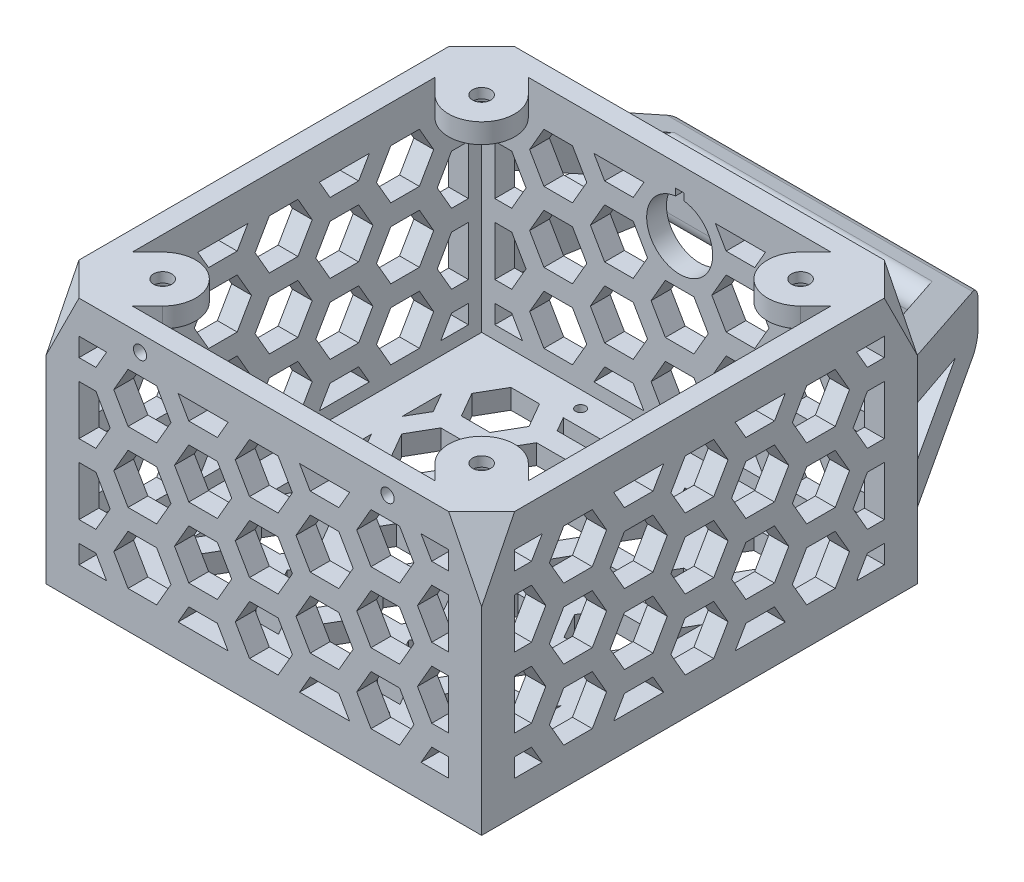
SolidWorks part; units mm, degrees
ref_plane "Front Plane" through (0, 0, 0) normal (0, 0, 1) x (1, 0, 0)
ref_plane "Top Plane" through (0, 0, 0) normal (0, 1, 0) x (1, 0, 0)
ref_plane "Right Plane" through (0, 0, 0) normal (1, 0, 0) x (0, 0, -1)
sketch "Sketch1" plane through (0, 0, 0) normal (0, 1, 0) x (1, 0, 0)
  line L0 (50, -50) -> (50, 50) construction
  line L1 (60, -60) -> (-60, -60)
  line L2 (60, -60) -> (60, 60)
  line L3 (60, 60) -> (-60, 60)
  line L4 (-60, -60) -> (-60, 60)
  line L5 (60, -60) -> (-60, 60) construction
  line L6 (60, 60) -> (-60, -60) construction
  line L7 (50, 50) -> (-50, 50) construction
  line L8 (-50, -50) -> (-50, 50) construction
  line L9 (50, -50) -> (-50, -50) construction
  line L10 (8.6603, 21.25) -> (4.3301, 28.75)
  line L11 (8.6603, 0) -> (4.3301, 7.5)
  line L12 (4.3301, 7.5) -> (-4.3301, 7.5)
  line L13 (-4.3301, 7.5) -> (-8.6603, 0)
  line L14 (-8.6603, 0) -> (-4.3301, -7.5)
  line L15 (-4.3301, -7.5) -> (4.3301, -7.5)
  line L16 (4.3301, -7.5) -> (8.6603, 0)
  line L17 (4.3301, 28.75) -> (-4.3301, 28.75)
  line L18 (-4.3301, 28.75) -> (-8.6603, 21.25)
  line L19 (-8.6603, 21.25) -> (-4.3301, 13.75)
  line L20 (-4.3301, 13.75) -> (4.3301, 13.75)
  line L21 (4.3301, 13.75) -> (8.6603, 21.25)
  line L22 (8.6603, 42.5) -> (4.3301, 50)
  line L23 (4.3301, 50) -> (-4.3301, 50)
  line L24 (-4.3301, 50) -> (-8.6603, 42.5)
  line L25 (-8.6603, 42.5) -> (-4.3301, 35)
  line L26 (-4.3301, 35) -> (4.3301, 35)
  line L27 (4.3301, 35) -> (8.6603, 42.5)
  line L28 (8.6603, -21.25) -> (4.3301, -13.75)
  line L29 (4.3301, -13.75) -> (-4.3301, -13.75)
  line L30 (-4.3301, -13.75) -> (-8.6603, -21.25)
  line L31 (-8.6603, -21.25) -> (-4.3301, -28.75)
  line L32 (-4.3301, -28.75) -> (4.3301, -28.75)
  line L33 (4.3301, -28.75) -> (8.6603, -21.25)
  line L34 (8.6603, -42.5) -> (4.3301, -35)
  line L35 (4.3301, -35) -> (-4.3301, -35)
  line L36 (-4.3301, -35) -> (-8.6603, -42.5)
  line L37 (-8.6603, -42.5) -> (-4.3301, -50)
  line L38 (-4.3301, -50) -> (4.3301, -50)
  line L39 (4.3301, -50) -> (8.6603, -42.5)
  line L40 (0, 13.75) -> (0, 7.5) construction
  line L41 (0, 10.625) -> (50, 10.625) construction
  line L42 (27.0633, 31.875) -> (22.7332, 39.375)
  line L43 (27.0633, 10.625) -> (22.7332, 18.125)
  line L44 (22.7332, 18.125) -> (14.0729, 18.125)
  line L45 (14.0729, 18.125) -> (9.7428, 10.625)
  line L46 (9.7428, 10.625) -> (14.0729, 3.125)
  line L47 (14.0729, 3.125) -> (22.7332, 3.125)
  line L48 (22.7332, 3.125) -> (27.0633, 10.625)
  line L49 (22.7332, 39.375) -> (14.0729, 39.375)
  line L50 (14.0729, 39.375) -> (9.7428, 31.875)
  line L51 (9.7428, 31.875) -> (14.0729, 24.375)
  line L52 (14.0729, 24.375) -> (22.7332, 24.375)
  line L53 (22.7332, 24.375) -> (27.0633, 31.875)
  line L57 (11.547, 50) -> (14.0729, 45.625)
  line L58 (14.0729, 45.625) -> (22.7332, 45.625)
  line L59 (22.7332, 45.625) -> (25.2591, 50)
  line L60 (22.7332, 60.625) -> (14.0729, 60.625)
  line L61 (14.0729, 60.625) -> (13.7121, 60)
  line L62 (23.094, 60) -> (22.7332, 60.625)
  line L63 (11.547, 50) -> (25.2591, 50)
  line L64 (-60, 0) -> (60, 0) construction
  line L65 (0, 60) -> (0, -60) construction
  line L66 (11.547, -50) -> (14.0729, -45.625)
  line L67 (14.0729, -45.625) -> (22.7332, -45.625)
  line L68 (22.7332, -45.625) -> (25.2591, -50)
  line L69 (11.547, -50) -> (25.2591, -50)
  line L70 (22.7332, -24.375) -> (27.0633, -31.875)
  line L71 (14.0729, -24.375) -> (22.7332, -24.375)
  line L72 (9.7428, -31.875) -> (14.0729, -24.375)
  line L73 (14.0729, -39.375) -> (9.7428, -31.875)
  line L74 (22.7332, -39.375) -> (14.0729, -39.375)
  line L75 (27.0633, -31.875) -> (22.7332, -39.375)
  line L76 (22.7332, -3.125) -> (27.0633, -10.625)
  line L77 (14.0729, -3.125) -> (22.7332, -3.125)
  line L78 (9.7428, -10.625) -> (14.0729, -3.125)
  line L79 (14.0729, -18.125) -> (9.7428, -10.625)
  line L80 (22.7332, -18.125) -> (14.0729, -18.125)
  line L81 (27.0633, -10.625) -> (22.7332, -18.125)
  line L82 (45.4663, 42.5) -> (41.1362, 50)
  line L83 (41.1362, 50) -> (32.476, 50)
  line L84 (32.476, 50) -> (28.1458, 42.5)
  line L85 (28.1458, 42.5) -> (32.476, 35)
  line L86 (32.476, 35) -> (41.1362, 35)
  line L87 (41.1362, 35) -> (45.4663, 42.5)
  line L88 (45.4663, 21.25) -> (41.1362, 28.75)
  line L89 (41.1362, 28.75) -> (32.476, 28.75)
  line L90 (32.476, 28.75) -> (28.1458, 21.25)
  line L91 (28.1458, 21.25) -> (32.476, 13.75)
  line L92 (32.476, 13.75) -> (41.1362, 13.75)
  line L93 (41.1362, 13.75) -> (45.4663, 21.25)
  line L94 (45.4663, 0) -> (41.1362, 7.5)
  line L95 (41.1362, 7.5) -> (32.476, 7.5)
  line L96 (32.476, 7.5) -> (28.1458, 0)
  line L97 (28.1458, 0) -> (32.476, -7.5)
  line L98 (32.476, -7.5) -> (41.1362, -7.5)
  line L99 (41.1362, -7.5) -> (45.4663, 0)
  line L100 (45.4663, -21.25) -> (41.1362, -13.75)
  line L101 (41.1362, -13.75) -> (32.476, -13.75)
  line L102 (32.476, -13.75) -> (28.1458, -21.25)
  line L103 (28.1458, -21.25) -> (32.476, -28.75)
  line L104 (32.476, -28.75) -> (41.1362, -28.75)
  line L105 (41.1362, -28.75) -> (45.4663, -21.25)
  line L106 (45.4663, -42.5) -> (41.1362, -35)
  line L107 (41.1362, -35) -> (32.476, -35)
  line L108 (32.476, -35) -> (28.1458, -42.5)
  line L109 (28.1458, -42.5) -> (32.476, -50)
  line L110 (32.476, -50) -> (41.1362, -50)
  line L111 (41.1362, -50) -> (45.4663, -42.5)
  line L118 (50, 37.8525) -> (46.5489, 31.875)
  line L119 (46.5489, 31.875) -> (50, 25.8975)
  line L124 (50, 16.6025) -> (46.5489, 10.625)
  line L125 (46.5489, 10.625) -> (50, 4.6475)
  line L131 (50, -16.6025) -> (46.5489, -10.625)
  line L132 (46.5489, -10.625) -> (50, -4.6475)
  line L137 (50, -37.8525) -> (46.5489, -31.875)
  line L138 (46.5489, -31.875) -> (50, -25.8975)
  line L144 (50, 37.8525) -> (50, 25.8975)
  line L145 (50.879, 45.625) -> (59.5392, 45.625)
  line L146 (59.5392, 45.625) -> (60, 46.423)
  line L147 (50.879, 24.375) -> (59.5392, 24.375)
  line L148 (59.5392, 39.375) -> (50.879, 39.375)
  line L149 (63.8694, 31.875) -> (60, 38.577)
  line L150 (60, 25.173) -> (63.8694, 31.875)
  line L151 (59.5392, 18.125) -> (50.879, 18.125)
  line L152 (50.879, 3.125) -> (59.5392, 3.125)
  line L153 (63.8694, 10.625) -> (60, 17.327)
  line L154 (59.5392, 3.125) -> (60, 3.923)
  line L155 (59.5392, -18.125) -> (50.879, -18.125)
  line L156 (50.879, -3.125) -> (59.5392, -3.125)
  line L157 (60, -3.923) -> (63.8694, -10.625)
  line L158 (60, -17.327) -> (59.5392, -18.125)
  line L159 (59.5392, -39.375) -> (50.879, -39.375)
  line L160 (50.879, -24.375) -> (59.5392, -24.375)
  line L161 (60, -25.173) -> (63.8694, -31.875)
  line L162 (63.8694, -31.875) -> (60, -38.577)
  line L163 (50.879, -45.625) -> (59.5392, -45.625)
  line L164 (59.5392, -45.625) -> (60, -46.423)
  line L165 (48.3531, 50) -> (50, 47.1475)
  line L166 (47.1304, 50) -> (50, 50)
  line L167 (50, 16.6025) -> (50, 4.6475)
  line L168 (50, -4.6475) -> (50, -16.6025)
  line L169 (50, -25.8975) -> (50, -37.8525)
  line L170 (-46.5489, -31.875) -> (-50, -25.8975)
  line L171 (48.3531, -50) -> (48.9559, -48.9559)
  line L172 (48.3531, -50) -> (50, -50)
  line L173 (-50, -37.8525) -> (-46.5489, -31.875)
  line L174 (-50, -25.8975) -> (-50, -37.8525)
  line L175 (-46.5489, -10.625) -> (-50, -4.6475)
  line L176 (-50, -16.6025) -> (-46.5489, -10.625)
  line L177 (-50, -4.6475) -> (-50, -16.6025)
  line L178 (-50, 16.6025) -> (-46.5489, 10.625)
  line L179 (-46.5489, 10.625) -> (-50, 4.6475)
  line L180 (-50, 16.6025) -> (-50, 4.6475)
  line L181 (-50, 37.8525) -> (-46.5489, 31.875)
  line L182 (-46.5489, 31.875) -> (-50, 25.8975)
  line L183 (-50, 37.8525) -> (-50, 25.8975)
  line L184 (-41.1362, 35) -> (-45.4663, 42.5)
  line L185 (-32.476, 35) -> (-41.1362, 35)
  line L186 (-28.1458, 42.5) -> (-32.476, 35)
  line L187 (-32.476, 50) -> (-28.1458, 42.5)
  line L188 (-41.1362, 50) -> (-32.476, 50)
  line L189 (-45.4663, 42.5) -> (-41.1362, 50)
  line L190 (-41.1362, 13.75) -> (-45.4663, 21.25)
  line L191 (-32.476, 13.75) -> (-41.1362, 13.75)
  line L192 (-28.1458, 21.25) -> (-32.476, 13.75)
  line L193 (-32.476, 28.75) -> (-28.1458, 21.25)
  line L194 (-41.1362, 28.75) -> (-32.476, 28.75)
  line L195 (-45.4663, 21.25) -> (-41.1362, 28.75)
  line L196 (-41.1362, -7.5) -> (-45.4663, 0)
  line L197 (-32.476, -7.5) -> (-41.1362, -7.5)
  line L198 (-28.1458, 0) -> (-32.476, -7.5)
  line L199 (-32.476, 7.5) -> (-28.1458, 0)
  line L200 (-41.1362, 7.5) -> (-32.476, 7.5)
  line L201 (-45.4663, 0) -> (-41.1362, 7.5)
  line L202 (-41.1362, -28.75) -> (-45.4663, -21.25)
  line L203 (-32.476, -28.75) -> (-41.1362, -28.75)
  line L204 (-28.1458, -21.25) -> (-32.476, -28.75)
  line L205 (-32.476, -13.75) -> (-28.1458, -21.25)
  line L206 (-41.1362, -13.75) -> (-32.476, -13.75)
  line L207 (-45.4663, -21.25) -> (-41.1362, -13.75)
  line L208 (-41.1362, -50) -> (-45.4663, -42.5)
  line L209 (-32.476, -50) -> (-41.1362, -50)
  line L210 (-28.1458, -42.5) -> (-32.476, -50)
  line L211 (-32.476, -35) -> (-28.1458, -42.5)
  line L212 (-41.1362, -35) -> (-32.476, -35)
  line L213 (-45.4663, -42.5) -> (-41.1362, -35)
  line L214 (-11.547, -50) -> (-25.2591, -50)
  line L215 (-22.7332, -45.625) -> (-25.2591, -50)
  line L216 (-14.0729, -45.625) -> (-22.7332, -45.625)
  line L217 (-11.547, -50) -> (-14.0729, -45.625)
  line L218 (-14.0729, -24.375) -> (-22.7332, -24.375)
  line L219 (-9.7428, -31.875) -> (-14.0729, -24.375)
  line L220 (-14.0729, -39.375) -> (-9.7428, -31.875)
  line L221 (-22.7332, -39.375) -> (-14.0729, -39.375)
  line L222 (-27.0633, -31.875) -> (-22.7332, -39.375)
  line L223 (-22.7332, -24.375) -> (-27.0633, -31.875)
  line L224 (-14.0729, -3.125) -> (-22.7332, -3.125)
  line L225 (-9.7428, -10.625) -> (-14.0729, -3.125)
  line L226 (-14.0729, -18.125) -> (-9.7428, -10.625)
  line L227 (-22.7332, -18.125) -> (-14.0729, -18.125)
  line L228 (-27.0633, -10.625) -> (-22.7332, -18.125)
  line L229 (-22.7332, -3.125) -> (-27.0633, -10.625)
  line L230 (-22.7332, 3.125) -> (-27.0633, 10.625)
  line L231 (-14.0729, 3.125) -> (-22.7332, 3.125)
  line L232 (-9.7428, 10.625) -> (-14.0729, 3.125)
  line L233 (-14.0729, 18.125) -> (-9.7428, 10.625)
  line L234 (-22.7332, 18.125) -> (-14.0729, 18.125)
  line L235 (-27.0633, 10.625) -> (-22.7332, 18.125)
  line L236 (-11.547, 50) -> (-14.0729, 45.625)
  line L237 (-14.0729, 45.625) -> (-22.7332, 45.625)
  line L238 (-22.7332, 45.625) -> (-25.2591, 50)
  line L239 (-11.547, 50) -> (-25.2591, 50)
  line L240 (-22.7332, 24.375) -> (-27.0633, 31.875)
  line L241 (-14.0729, 24.375) -> (-22.7332, 24.375)
  line L242 (-9.7428, 31.875) -> (-14.0729, 24.375)
  line L243 (-14.0729, 39.375) -> (-9.7428, 31.875)
  line L244 (-22.7332, 39.375) -> (-14.0729, 39.375)
  line L245 (-27.0633, 31.875) -> (-22.7332, 39.375)
  circle A0 centre (0, 0) radius 7.5 construction
  circle A1 centre (18.403, 10.625) radius 7.5 construction
  point P0 (0, 0)
  point P265 (0, 0)
  dimension "D1" = 120
  dimension "D2" = 120
  dimension "D4" = 15
  dimension "D6" = 0
  dimension "D7" = 3
  dimension "D8" = 0
  dimension "D9" = 15
  dimension "D10" = 6.25
  dimension "D12" = 6.25
  dimension "D14" = 6.25
  dimension "D16" = 6.25
  dimension "D3" = 10
  dimension "D5" = 3
  dimension "D11" = 3
  dimension "D13" = 2
  dimension "D15" = 2
extrude "Boss-Extrude2" add sketch "Sketch1" along normal blind 6
sketch "Sketch2" plane through (0, 0, 60) normal (0, 0, 1) x (1, 0, 0)
  line L0 (0, 0) -> (0, 80) construction
  line L1 (-66, 40) -> (66, 40) construction
  line L2 (66, 80) -> (-66, 80)
  line L3 (66, 80) -> (66, 0)
  line L4 (66, 0) -> (-66, 0)
  line L5 (-66, 80) -> (-66, 0)
  line L6 (66, 80) -> (-66, 0) construction
  line L7 (66, 0) -> (-66, 80) construction
  line L8 (56, 70) -> (56, 10) construction
  line L9 (56, 10) -> (-56, 10) construction
  line L10 (-56, 70) -> (-56, 10) construction
  line L11 (56, 70) -> (-56, 70) construction
  line L12 (8.6603, 61.25) -> (4.3301, 68.75)
  line L13 (8.6603, 40) -> (4.3301, 47.5)
  line L14 (4.3301, 47.5) -> (-4.3301, 47.5)
  line L15 (-4.3301, 47.5) -> (-8.6603, 40)
  line L16 (-8.6603, 40) -> (-4.3301, 32.5)
  line L17 (-4.3301, 32.5) -> (4.3301, 32.5)
  line L18 (4.3301, 32.5) -> (8.6603, 40)
  line L19 (4.3301, 68.75) -> (-4.3301, 68.75)
  line L20 (-4.3301, 68.75) -> (-8.6603, 61.25)
  line L21 (-8.6603, 61.25) -> (-4.3301, 53.75)
  line L22 (-4.3301, 53.75) -> (4.3301, 53.75)
  line L23 (4.3301, 53.75) -> (8.6603, 61.25)
  line L24 (4.3301, 26.25) -> (8.6603, 18.75)
  line L25 (-4.3301, 26.25) -> (4.3301, 26.25)
  line L26 (-8.6603, 18.75) -> (-4.3301, 26.25)
  line L27 (-4.3301, 11.25) -> (-8.6603, 18.75)
  line L28 (4.3301, 11.25) -> (-4.3301, 11.25)
  line L29 (8.6603, 18.75) -> (4.3301, 11.25)
  line L30 (0, 53.75) -> (0, 47.5) construction
  line L31 (0, 50.625) -> (56, 50.625) construction
  line L32 (-60, 6) -> (-60, 0) construction
  line L33 (27.0633, 50.625) -> (22.7332, 58.125)
  line L34 (22.7332, 58.125) -> (14.0729, 58.125)
  line L35 (14.0729, 58.125) -> (9.7428, 50.625)
  line L36 (9.7428, 50.625) -> (14.0729, 43.125)
  line L37 (14.0729, 43.125) -> (22.7332, 43.125)
  line L38 (22.7332, 43.125) -> (27.0633, 50.625)
  line L39 (-60, 0) -> (60, 0) construction
  line L43 (10.8253, 70) -> (14.0729, 64.375)
  line L44 (14.0729, 64.375) -> (22.7332, 64.375)
  line L45 (22.7332, 64.375) -> (25.9808, 70)
  line L46 (14.0729, 79.375) -> (9.7428, 71.875)
  line L47 (22.7332, 79.375) -> (14.0729, 79.375)
  line L48 (27.0633, 71.875) -> (22.7332, 79.375)
  line L49 (10.8253, 70) -> (25.9808, 70)
  line L50 (22.7332, 36.875) -> (27.0633, 29.375)
  line L51 (14.0729, 36.875) -> (22.7332, 36.875)
  line L52 (9.7428, 29.375) -> (14.0729, 36.875)
  line L53 (14.0729, 21.875) -> (9.7428, 29.375)
  line L54 (22.7332, 21.875) -> (14.0729, 21.875)
  line L55 (27.0633, 29.375) -> (22.7332, 21.875)
  line L56 (10.8253, 10) -> (14.0729, 15.625)
  line L57 (14.0729, 15.625) -> (22.7332, 15.625)
  line L58 (22.7332, 15.625) -> (25.9808, 10)
  line L59 (10.8253, 10) -> (25.9808, 10)
  line L60 (45.4663, 61.25) -> (41.1362, 68.75)
  line L61 (41.1362, 68.75) -> (32.476, 68.75)
  line L62 (32.476, 68.75) -> (28.1458, 61.25)
  line L63 (28.1458, 61.25) -> (32.476, 53.75)
  line L64 (32.476, 53.75) -> (41.1362, 53.75)
  line L65 (41.1362, 53.75) -> (45.4663, 61.25)
  line L66 (45.4663, 40) -> (41.1362, 47.5)
  line L67 (41.1362, 47.5) -> (32.476, 47.5)
  line L68 (32.476, 47.5) -> (28.1458, 40)
  line L69 (28.1458, 40) -> (32.476, 32.5)
  line L70 (32.476, 32.5) -> (41.1362, 32.5)
  line L71 (41.1362, 32.5) -> (45.4663, 40)
  line L72 (41.1362, 26.25) -> (45.4663, 18.75)
  line L73 (45.4663, 18.75) -> (41.1362, 11.25)
  line L74 (41.1362, 11.25) -> (32.476, 11.25)
  line L75 (32.476, 11.25) -> (28.1458, 18.75)
  line L76 (28.1458, 18.75) -> (32.476, 26.25)
  line L77 (32.476, 26.25) -> (41.1362, 26.25)
  line L78 (47.6314, 70) -> (56, 70)
  line L80 (50.879, 64.375) -> (56, 64.375)
  line L81 (47.6314, 70) -> (50.879, 64.375)
  line L83 (56, 58.125) -> (50.879, 58.125)
  line L84 (50.879, 58.125) -> (46.5489, 50.625)
  line L85 (46.5489, 50.625) -> (50.879, 43.125)
  line L86 (50.879, 43.125) -> (56, 43.125)
  line L90 (56, 21.875) -> (50.879, 21.875)
  line L91 (50.879, 21.875) -> (46.5489, 29.375)
  line L92 (46.5489, 29.375) -> (50.879, 36.875)
  line L93 (50.879, 36.875) -> (56, 36.875)
  line L94 (47.6314, 10) -> (50.879, 15.625)
  line L95 (50.879, 15.625) -> (56, 15.625)
  line L97 (47.6314, 10) -> (56, 10)
  line L98 (59.5392, 64.375) -> (62.7868, 70)
  line L99 (63.8694, 50.625) -> (59.5392, 58.125)
  line L100 (59.5392, 43.125) -> (63.8694, 50.625)
  line L101 (56, 70) -> (56, 64.375)
  line L102 (56, 58.125) -> (56, 43.125)
  line L103 (56, 36.875) -> (56, 21.875)
  line L104 (59.5392, 36.875) -> (63.8694, 29.375)
  line L105 (63.8694, 29.375) -> (59.5392, 21.875)
  line L106 (59.5392, 15.625) -> (62.7868, 10)
  line L107 (56, 15.625) -> (56, 10)
  line L108 (-50.879, 15.625) -> (-56, 15.625)
  line L109 (-47.6314, 10) -> (-50.879, 15.625)
  line L110 (-47.6314, 10) -> (-56, 10)
  line L111 (-56, 15.625) -> (-56, 10)
  line L112 (-50.879, 36.875) -> (-56, 36.875)
  line L113 (-46.5489, 29.375) -> (-50.879, 36.875)
  line L114 (-50.879, 21.875) -> (-46.5489, 29.375)
  line L115 (-56, 21.875) -> (-50.879, 21.875)
  line L116 (-56, 36.875) -> (-56, 21.875)
  line L117 (-56, 58.125) -> (-50.879, 58.125)
  line L118 (-50.879, 58.125) -> (-46.5489, 50.625)
  line L119 (-46.5489, 50.625) -> (-50.879, 43.125)
  line L120 (-50.879, 43.125) -> (-56, 43.125)
  line L121 (-56, 58.125) -> (-56, 43.125)
  line L122 (-47.6314, 70) -> (-56, 70)
  line L123 (-47.6314, 70) -> (-50.879, 64.375)
  line L124 (-50.879, 64.375) -> (-56, 64.375)
  line L125 (-56, 70) -> (-56, 64.375)
  line L126 (-41.1362, 53.75) -> (-45.4663, 61.25)
  line L127 (-32.476, 53.75) -> (-41.1362, 53.75)
  line L128 (-28.1458, 61.25) -> (-32.476, 53.75)
  line L129 (-32.476, 68.75) -> (-28.1458, 61.25)
  line L130 (-41.1362, 68.75) -> (-32.476, 68.75)
  line L131 (-45.4663, 61.25) -> (-41.1362, 68.75)
  line L132 (-41.1362, 32.5) -> (-45.4663, 40)
  line L133 (-32.476, 32.5) -> (-41.1362, 32.5)
  line L134 (-28.1458, 40) -> (-32.476, 32.5)
  line L135 (-32.476, 47.5) -> (-28.1458, 40)
  line L136 (-41.1362, 47.5) -> (-32.476, 47.5)
  line L137 (-45.4663, 40) -> (-41.1362, 47.5)
  line L138 (-32.476, 26.25) -> (-41.1362, 26.25)
  line L139 (-28.1458, 18.75) -> (-32.476, 26.25)
  line L140 (-32.476, 11.25) -> (-28.1458, 18.75)
  line L141 (-41.1362, 11.25) -> (-32.476, 11.25)
  line L142 (-45.4663, 18.75) -> (-41.1362, 11.25)
  line L143 (-41.1362, 26.25) -> (-45.4663, 18.75)
  line L144 (-10.8253, 10) -> (-25.9808, 10)
  line L145 (-22.7332, 15.625) -> (-25.9808, 10)
  line L146 (-14.0729, 15.625) -> (-22.7332, 15.625)
  line L147 (-10.8253, 10) -> (-14.0729, 15.625)
  line L148 (-14.0729, 36.875) -> (-22.7332, 36.875)
  line L149 (-9.7428, 29.375) -> (-14.0729, 36.875)
  line L150 (-14.0729, 21.875) -> (-9.7428, 29.375)
  line L151 (-22.7332, 21.875) -> (-14.0729, 21.875)
  line L152 (-27.0633, 29.375) -> (-22.7332, 21.875)
  line L153 (-22.7332, 36.875) -> (-27.0633, 29.375)
  line L154 (-22.7332, 43.125) -> (-27.0633, 50.625)
  line L155 (-14.0729, 43.125) -> (-22.7332, 43.125)
  line L156 (-9.7428, 50.625) -> (-14.0729, 43.125)
  line L157 (-14.0729, 58.125) -> (-9.7428, 50.625)
  line L158 (-22.7332, 58.125) -> (-14.0729, 58.125)
  line L159 (-27.0633, 50.625) -> (-22.7332, 58.125)
  line L160 (-10.8253, 70) -> (-14.0729, 64.375)
  line L161 (-14.0729, 64.375) -> (-22.7332, 64.375)
  line L162 (-22.7332, 64.375) -> (-25.9808, 70)
  line L163 (-10.8253, 70) -> (-25.9808, 70)
  circle A0 centre (0, 40) radius 7.5 construction
  circle A1 centre (18.403, 50.625) radius 7.5 construction
  point P3 (0, 40)
  dimension "D1" = 80
  dimension "D3" = 15
  dimension "D5" = 6.25
  dimension "D6" = 15
  dimension "D7" = 6.25
  dimension "D8" = 6
  dimension "D10" = 6.25
  dimension "D12" = 6.25
  dimension "D14" = 6.25
  dimension "D2" = 10
  dimension "D4" = 2
  dimension "D9" = 2
  dimension "D11" = 2
  dimension "D13" = 2
extrude "Boss-Extrude3" add sketch "Sketch2" along normal blind 6
mirror "Mirror1" about plane through (0, 0, 0) normal (0, 0, 1) of "Boss-Extrude3"
sketch "Sketch3" plane through (-60, 0, 0) normal (-1, 0, 0) x (0, 0, 1)
  line L0 (-66, 80) -> (66, 80) construction
  line L1 (66, 80) -> (66, 0) construction
  line L2 (0, 0) -> (0, 80) construction
  line L3 (-66, 80) -> (-66, 0) construction
  line L4 (60, 0) -> (-60, 0)
  line L5 (60, 0) -> (60, 80)
  line L6 (60, 80) -> (-60, 80)
  line L7 (-60, 0) -> (-60, 80)
  line L8 (60, 0) -> (-60, 80) construction
  line L9 (60, 80) -> (-60, 0) construction
  line L10 (56, 10) -> (-56, 10) construction
  line L11 (56, 10) -> (56, 70) construction
  line L12 (56, 70) -> (-56, 70) construction
  line L13 (-56, 10) -> (-56, 70) construction
  line L14 (56, 10) -> (-56, 70) construction
  line L15 (56, 70) -> (-56, 10) construction
  line L16 (-66, 40) -> (66, 40) construction
  line L17 (8.6603, 40) -> (4.3301, 47.5)
  line L18 (4.3301, 47.5) -> (-4.3301, 47.5)
  line L19 (-4.3301, 47.5) -> (-8.6603, 40)
  line L20 (-8.6603, 40) -> (-4.3301, 32.5)
  line L21 (-4.3301, 32.5) -> (4.3301, 32.5)
  line L22 (4.3301, 32.5) -> (8.6603, 40)
  line L23 (8.6603, 61.25) -> (4.3301, 68.75)
  line L24 (4.3301, 68.75) -> (-4.3301, 68.75)
  line L25 (-4.3301, 68.75) -> (-8.6603, 61.25)
  line L26 (-8.6603, 61.25) -> (-4.3301, 53.75)
  line L27 (-4.3301, 53.75) -> (4.3301, 53.75)
  line L28 (4.3301, 53.75) -> (8.6603, 61.25)
  line L29 (4.3301, 26.25) -> (8.6603, 18.75)
  line L30 (-4.3301, 26.25) -> (4.3301, 26.25)
  line L31 (-8.6603, 18.75) -> (-4.3301, 26.25)
  line L32 (-4.3301, 11.25) -> (-8.6603, 18.75)
  line L33 (4.3301, 11.25) -> (-4.3301, 11.25)
  line L34 (8.6603, 18.75) -> (4.3301, 11.25)
  line L35 (0, 53.75) -> (0, 47.5) construction
  line L36 (0, 50.625) -> (56, 50.625) construction
  line L38 (27.0633, 50.625) -> (22.7332, 58.125)
  line L39 (22.7332, 58.125) -> (14.0729, 58.125)
  line L40 (14.0729, 58.125) -> (9.7428, 50.625)
  line L41 (9.7428, 50.625) -> (14.0729, 43.125)
  line L42 (14.0729, 43.125) -> (22.7332, 43.125)
  line L43 (22.7332, 43.125) -> (27.0633, 50.625)
  line L46 (10.8253, 70) -> (14.0729, 64.375)
  line L47 (14.0729, 64.375) -> (22.7332, 64.375)
  line L48 (22.7332, 64.375) -> (25.9808, 70)
  line L49 (14.0729, 79.375) -> (9.7428, 71.875)
  line L50 (22.7332, 79.375) -> (14.0729, 79.375)
  line L51 (27.0633, 71.875) -> (22.7332, 79.375)
  line L52 (10.8253, 70) -> (25.9808, 70)
  line L53 (22.7332, 36.875) -> (27.0633, 29.375)
  line L54 (14.0729, 36.875) -> (22.7332, 36.875)
  line L55 (9.7428, 29.375) -> (14.0729, 36.875)
  line L56 (14.0729, 21.875) -> (9.7428, 29.375)
  line L57 (22.7332, 21.875) -> (14.0729, 21.875)
  line L58 (27.0633, 29.375) -> (22.7332, 21.875)
  line L59 (10.8253, 10) -> (14.0729, 15.625)
  line L60 (14.0729, 15.625) -> (22.7332, 15.625)
  line L61 (22.7332, 15.625) -> (25.9808, 10)
  line L62 (10.8253, 10) -> (25.9808, 10)
  line L63 (45.4663, 61.25) -> (41.1362, 68.75)
  line L64 (41.1362, 68.75) -> (32.476, 68.75)
  line L65 (32.476, 68.75) -> (28.1458, 61.25)
  line L66 (28.1458, 61.25) -> (32.476, 53.75)
  line L67 (32.476, 53.75) -> (41.1362, 53.75)
  line L68 (41.1362, 53.75) -> (45.4663, 61.25)
  line L69 (45.4663, 40) -> (41.1362, 47.5)
  line L70 (41.1362, 47.5) -> (32.476, 47.5)
  line L71 (32.476, 47.5) -> (28.1458, 40)
  line L72 (28.1458, 40) -> (32.476, 32.5)
  line L73 (32.476, 32.5) -> (41.1362, 32.5)
  line L74 (41.1362, 32.5) -> (45.4663, 40)
  line L75 (41.1362, 26.25) -> (45.4663, 18.75)
  line L76 (45.4663, 18.75) -> (41.1362, 11.25)
  line L77 (41.1362, 11.25) -> (32.476, 11.25)
  line L78 (32.476, 11.25) -> (28.1458, 18.75)
  line L79 (28.1458, 18.75) -> (32.476, 26.25)
  line L80 (32.476, 26.25) -> (41.1362, 26.25)
  line L81 (47.6314, 70) -> (56, 70)
  line L83 (50.879, 64.375) -> (56, 64.375)
  line L84 (47.6314, 70) -> (50.879, 64.375)
  line L86 (56, 58.125) -> (50.879, 58.125)
  line L87 (50.879, 58.125) -> (46.5489, 50.625)
  line L88 (46.5489, 50.625) -> (50.879, 43.125)
  line L89 (50.879, 43.125) -> (56, 43.125)
  line L93 (56, 21.875) -> (50.879, 21.875)
  line L94 (50.879, 21.875) -> (46.5489, 29.375)
  line L95 (46.5489, 29.375) -> (50.879, 36.875)
  line L96 (50.879, 36.875) -> (56, 36.875)
  line L97 (47.6314, 10) -> (50.879, 15.625)
  line L98 (50.879, 15.625) -> (56, 15.625)
  line L100 (47.6314, 10) -> (56, 10)
  line L101 (56, 15.625) -> (56, 10)
  line L102 (60, 65.173) -> (62.7868, 70)
  line L103 (63.8694, 50.625) -> (60, 57.327)
  line L104 (59.5392, 43.125) -> (60, 43.923)
  line L105 (60, 36.077) -> (63.8694, 29.375)
  line L106 (60, 22.673) -> (59.5392, 21.875)
  line L107 (60, 14.827) -> (62.7868, 10)
  line L108 (56, 36.875) -> (56, 21.875)
  line L109 (56, 58.125) -> (56, 43.125)
  line L110 (56, 70) -> (56, 64.375)
  line L111 (-50.879, 15.625) -> (-56, 15.625)
  line L112 (-47.6314, 10) -> (-50.879, 15.625)
  line L113 (-47.6314, 10) -> (-56, 10)
  line L114 (-56, 15.625) -> (-56, 10)
  line L115 (-50.879, 36.875) -> (-56, 36.875)
  line L116 (-46.5489, 29.375) -> (-50.879, 36.875)
  line L117 (-50.879, 21.875) -> (-46.5489, 29.375)
  line L118 (-56, 21.875) -> (-50.879, 21.875)
  line L119 (-56, 36.875) -> (-56, 21.875)
  line L120 (-56, 58.125) -> (-50.879, 58.125)
  line L121 (-50.879, 58.125) -> (-46.5489, 50.625)
  line L122 (-46.5489, 50.625) -> (-50.879, 43.125)
  line L123 (-50.879, 43.125) -> (-56, 43.125)
  line L124 (-56, 58.125) -> (-56, 43.125)
  line L125 (-47.6314, 70) -> (-56, 70)
  line L126 (-47.6314, 70) -> (-50.879, 64.375)
  line L127 (-50.879, 64.375) -> (-56, 64.375)
  line L128 (-56, 70) -> (-56, 64.375)
  line L129 (-41.1362, 53.75) -> (-45.4663, 61.25)
  line L130 (-32.476, 53.75) -> (-41.1362, 53.75)
  line L131 (-28.1458, 61.25) -> (-32.476, 53.75)
  line L132 (-32.476, 68.75) -> (-28.1458, 61.25)
  line L133 (-41.1362, 68.75) -> (-32.476, 68.75)
  line L134 (-45.4663, 61.25) -> (-41.1362, 68.75)
  line L135 (-41.1362, 32.5) -> (-45.4663, 40)
  line L136 (-32.476, 32.5) -> (-41.1362, 32.5)
  line L137 (-28.1458, 40) -> (-32.476, 32.5)
  line L138 (-32.476, 47.5) -> (-28.1458, 40)
  line L139 (-41.1362, 47.5) -> (-32.476, 47.5)
  line L140 (-45.4663, 40) -> (-41.1362, 47.5)
  line L141 (-32.476, 26.25) -> (-41.1362, 26.25)
  line L142 (-28.1458, 18.75) -> (-32.476, 26.25)
  line L143 (-32.476, 11.25) -> (-28.1458, 18.75)
  line L144 (-41.1362, 11.25) -> (-32.476, 11.25)
  line L145 (-45.4663, 18.75) -> (-41.1362, 11.25)
  line L146 (-41.1362, 26.25) -> (-45.4663, 18.75)
  line L147 (-10.8253, 10) -> (-25.9808, 10)
  line L148 (-22.7332, 15.625) -> (-25.9808, 10)
  line L149 (-14.0729, 15.625) -> (-22.7332, 15.625)
  line L150 (-10.8253, 10) -> (-14.0729, 15.625)
  line L151 (-14.0729, 36.875) -> (-22.7332, 36.875)
  line L152 (-9.7428, 29.375) -> (-14.0729, 36.875)
  line L153 (-14.0729, 21.875) -> (-9.7428, 29.375)
  line L154 (-22.7332, 21.875) -> (-14.0729, 21.875)
  line L155 (-27.0633, 29.375) -> (-22.7332, 21.875)
  line L156 (-22.7332, 36.875) -> (-27.0633, 29.375)
  line L157 (-22.7332, 43.125) -> (-27.0633, 50.625)
  line L158 (-14.0729, 43.125) -> (-22.7332, 43.125)
  line L159 (-9.7428, 50.625) -> (-14.0729, 43.125)
  line L160 (-14.0729, 58.125) -> (-9.7428, 50.625)
  line L161 (-22.7332, 58.125) -> (-14.0729, 58.125)
  line L162 (-27.0633, 50.625) -> (-22.7332, 58.125)
  line L163 (-10.8253, 70) -> (-14.0729, 64.375)
  line L164 (-14.0729, 64.375) -> (-22.7332, 64.375)
  line L165 (-22.7332, 64.375) -> (-25.9808, 70)
  line L166 (-10.8253, 70) -> (-25.9808, 70)
  circle A0 centre (0, 40) radius 7.5 construction
  circle A1 centre (18.403, 50.625) radius 7.5 construction
  point P8 (0, 40)
  point P14 (0, 40)
  dimension "D1" = 10
  dimension "D2" = 10
  dimension "D3" = 15
  dimension "D5" = 6.25
  dimension "D6" = 15
  dimension "D7" = 6.25
  dimension "D9" = 6.25
  dimension "D11" = 6.25
  dimension "D13" = 6.25
  dimension "D4" = 2
  dimension "D8" = 2
  dimension "D10" = 2
  dimension "D12" = 2
extrude "Boss-Extrude4" add sketch "Sketch3" along normal blind 6
mirror "Mirror2" about plane through (0, 0, 0) normal (1, 0, 0) of "Boss-Extrude4"
sketch "Sketch4" plane through (0, 0, 0) normal (0, -1, 0) x (1, 0, 0)
  line L0 (-66, -66) -> (-44.4, -106)
  line L1 (-44.4, -106) -> (44.4, -106)
  line L2 (44.4, -106) -> (66, -66)
  line L3 (-56, -66) -> (-42.5, -91)
  line L4 (-66, -66) -> (66, -66) construction
  line L5 (-42.5, -91) -> (42.5, -91)
  line L6 (42.5, -91) -> (56, -66)
  line L7 (-66, -66) -> (-56, -66)
  line L8 (56, -66) -> (66, -66)
  dimension "D1" = 10
  dimension "D2" = 10
  dimension "D3" = 25
  dimension "D4" = 15
  dimension "D5" = 85
extrude "Boss-Extrude5" add sketch "Sketch4" along normal mid plane 40 from offset 40 contours L8 L2 L1 L0 L7 L3 L5 L6 offset against normal yes
sketch "Sketch5" plane through (0, 0, 0) normal (1, 0, 0) x (0, 0, -1)
  line L0 (66, 60) -> (106, 47.5)
  line L1 (106, 20) -> (106, 60) construction
  line L2 (106, 47.5) -> (106, 60)
  line L3 (106, 60) -> (66, 60)
  line L4 (66, 20) -> (106, 32.5)
  line L5 (106, 32.5) -> (106, 20)
  line L6 (106, 20) -> (66, 20)
  line L7 (66, 47.5) -> (66, 32.5)
  line L8 (66, 20) -> (66, 60) construction
  line L9 (66, 32.5) -> (91, 40)
  line L10 (91, 40) -> (66, 47.5)
  line L11 (106, 40) -> (66, 40) construction
  point P19 (66, 40)
  dimension "D1" = 15
  dimension "D2" = 15
  dimension "D3" = 15
extrude "Cut-Extrude2" cut sketch "Sketch5" against normal through all both and the other way through all contours L6 L5 L4 | L0 L2 L3 | L9 L10 L7
fillet "Fillet2" radius 5 1 edges at (0, 47.5, -106)
fillet "Fillet3" radius 5 1 edges at (0, 32.5, -106)
fillet "Fillet4" radius 5 1 edges at (0, 52.1875, -91)
fillet "Fillet5" radius 5 1 edges at (0, 27.8125, -91)
sketch "Sketch9" plane through (0, 0, 66) normal (0, 0, 1) x (1, 0, 0)
  line L0 (0, 80) -> (0, 0) construction
  line L1 (66, 80) -> (-66, 80) construction
  line L2 (-37.5, 75) -> (37.5, 75) construction
  line L3 (-10.8253, 70) -> (-25.9808, 70) construction
  circle A0 centre (-37.5, 75) radius 2
  circle A1 centre (37.5, 75) radius 2
  point P7 (0, 75)
  dimension "D1" = 4
  dimension "D2" = 4
  dimension "D3" = 75
  dimension "D4" = 5
extrude "Cut-Extrude3" cut sketch "Sketch9" against normal up to next and the other way through all
sketch "Sketch11" plane through (0, 80, 0) normal (0, 1, 0) x (1, 0, 0)
  line L0 (-66, 66) -> (0, 0) construction
  line L1 (-50.2669, 46.3778) -> (-55.3934, 41.2513) construction
  line L2 (-48.3223, 48.3223) -> (-50.2669, 46.3778) construction
  line L9 (-48.3223, 48.3223) -> (-46.3778, 50.2669) construction
  line L28 (-55.3934, 41.2513) -> (-60, 45.8579)
  line L30 (60, 60) -> (-60, 60) construction
  line L31 (-60, -60) -> (-60, 60) construction
  line L32 (-60, 45.8579) -> (-60, 60)
  line L33 (-60, 60) -> (-45.8579, 60)
  line L34 (-45.8579, 60) -> (-41.2513, 55.3934)
  line L35 (-46.3778, 50.2669) -> (-41.2513, 55.3934) construction
  line L36 (41.2513, 55.3934) -> (45.8579, 60)
  line L37 (45.8579, 60) -> (60, 60)
  line L38 (60, 60) -> (60, 45.8579)
  line L39 (60, 45.8579) -> (55.3934, 41.2513)
  line L40 (55.3934, -41.2513) -> (60, -45.8579)
  line L41 (60, -45.8579) -> (60, -60)
  line L42 (60, -60) -> (45.8579, -60)
  line L43 (45.8579, -60) -> (41.2513, -55.3934)
  line L44 (-41.2513, -55.3934) -> (-45.8579, -60)
  line L45 (-45.8579, -60) -> (-60, -60)
  line L46 (-60, -60) -> (-60, -45.8579)
  line L47 (-60, -45.8579) -> (-55.3934, -41.2513)
  arc A1 (-55.3934, 41.2513) -> (-41.2513, 55.3934) centre (-48.3223, 48.3223) ccw
  circle A5 centre (-48.3223, 48.3223) radius 2.75
  arc A6 (-55.3934, 55.3934) -> (-55.3934, 41.2513) centre (-48.3223, 48.3223) ccw construction
  arc A7 (-41.2513, 55.3934) -> (-55.3934, 55.3934) centre (-48.3223, 48.3223) ccw construction
  arc A8 (41.2513, 55.3934) -> (55.3934, 41.2513) centre (48.3223, 48.3223) ccw
  circle A9 centre (48.3223, 48.3223) radius 2.75
  arc A10 (55.3934, -41.2513) -> (41.2513, -55.3934) centre (48.3223, -48.3223) ccw
  circle A11 centre (48.3223, -48.3223) radius 2.75
  arc A12 (-41.2513, -55.3934) -> (-55.3934, -41.2513) centre (-48.3223, -48.3223) ccw
  circle A13 centre (-48.3223, -48.3223) radius 2.75
  point P45 (0, 0)
  dimension "D1" = 20
  dimension "D3" = 5.5
  dimension "D2" = 25
extrude "Boss-Extrude8" add sketch "Sketch11" against normal blind 6
sketch "Sketch12" plane through (0, 74, 0) normal (0, -1, 0) x (1, 0, 0)
  circle A5 centre (-48.3223, 48.3223) radius 6
  circle A6 centre (-48.3223, -48.3223) radius 6
  circle A7 centre (48.3223, -48.3223) radius 6
  circle A8 centre (48.3223, 48.3223) radius 6
  circle A9 centre (48.3223, 48.3223) radius 2.75 construction
  point P12 (0, 0)
  dimension "D1" = 12
extrude "Cut-Extrude4" cut sketch "Sketch12" against normal blind 3
sketch "Sketch13" plane through (0, 6, 0) normal (0, 1, 0) x (1, 0, 0)
  line L0 (45.8579, 60) -> (-45.8579, 60) construction
  line L1 (0, -126.5108) -> (0, 126.5108) construction
  line L2 (-126.5108, 0) -> (126.5108, 0) construction
  circle A0 centre (-25, 55) radius 1.5
  circle A1 centre (25, 55) radius 1.5
  circle A2 centre (25, -55) radius 1.5
  circle A3 centre (-25, -55) radius 1.5
  dimension "D3" = 3
  dimension "D1" = 5
  dimension "D2" = 35
extrude "Cut-Extrude5" cut sketch "Sketch13" against normal through all
sketch "Sketch14" plane through (0, 0, -66) normal (0, 0, -1) x (-1, 0, 0)
  line L0 (-8.6603, 61.25) -> (8.6603, 61.25) construction
  line L1 (0, 71.25) -> (0, 73.25) construction
  line L2 (0, 73.25) -> (-1.25, 73.25)
  line L3 (-1.25, 73.25) -> (-1.25, 71.1716)
  line L4 (0, 73.25) -> (1.25, 73.25)
  line L5 (1.25, 73.25) -> (1.25, 71.1716)
  arc A0 (-1.25, 71.1716) -> (1.25, 71.1716) centre (0, 61.25) ccw
  arc A1 (0, 71.25) -> (-1.25, 71.1716) centre (0, 61.25) ccw construction
  arc A2 (1.25, 71.1716) -> (0, 71.25) centre (0, 61.25) ccw construction
  dimension "D1" = 20
  dimension "D2" = 2
  dimension "D3" = 2.5
extrude "Cut-Extrude6" cut sketch "Sketch14" against normal up to next
sketch "Sketch15" plane through (0, 80, 0) normal (0, 1, 0) x (1, 0, 0)
  line L0 (-66, -66) -> (-73.2213, -73.2213) construction
ref_plane "Plane1" through (0, 0, 0) normal (-0.7071, 0, -0.7071) x (-0.7071, 0, 0.7071)
sketch "Sketch16" plane through (0, 0, 0) normal (-0.7071, 0, -0.7071) x (-0.7071, 0, 0.7071)
  line L0 (86.267, 70) -> (86.267, 80) construction
  line L1 (93.3381, 80) -> (0, 80) construction
  line L2 (86.267, 80) -> (93.3381, 80)
  line L3 (86.267, 80) -> (93.3381, 60)
  line L4 (93.3381, 80) -> (93.3381, 0) construction
  line L5 (93.3381, 60) -> (93.3381, 80)
  line L6 (0, 60) -> (93.3381, 60) construction
  point P11 (93.3381, 59.7139)
extrude "Cut-Extrude7" cut sketch "Sketch16" against normal through all both and the other way through all
mirror "Mirror3" about plane through (0, 0, 0) normal (1, 0, 0) of "Cut-Extrude7"
mirror "Mirror4" about plane through (0, 0, 0) normal (0, 0, 1) of "Cut-Extrude7", "Mirror3"
